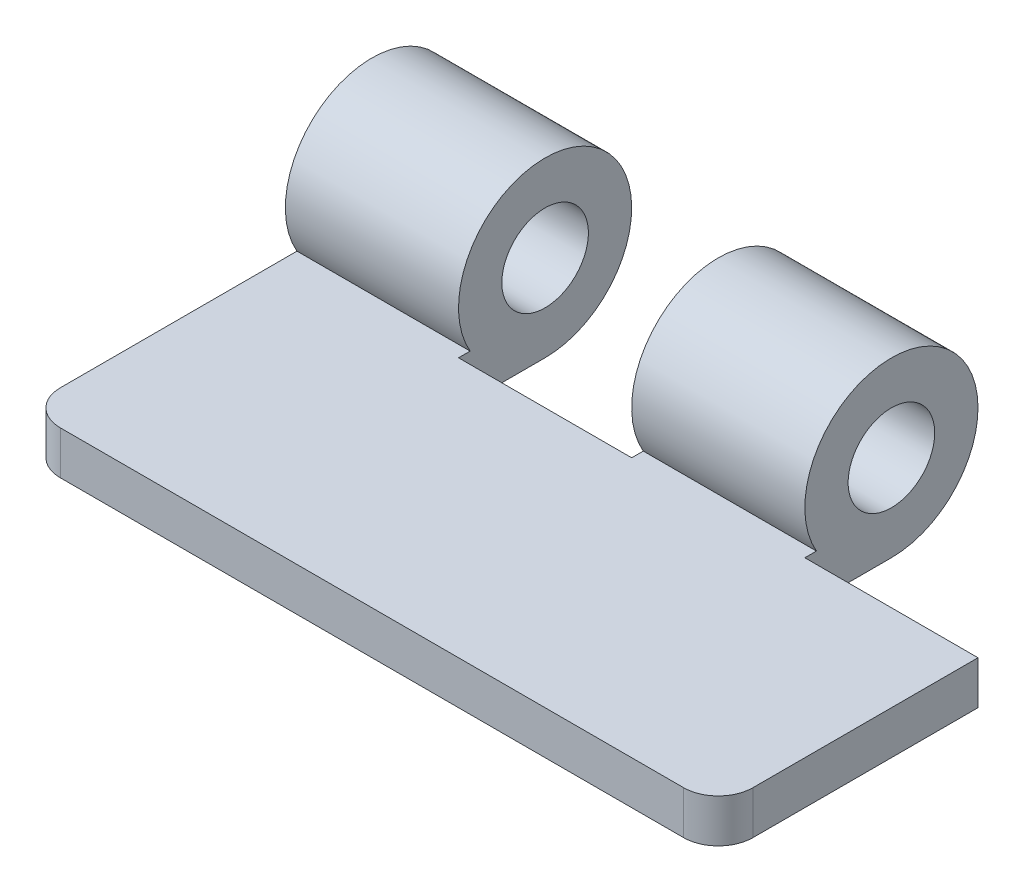
SolidWorks part; units mm, degrees
ref_plane "Front Plane" through (0, 0, 0) normal (0, 0, 1) x (1, 0, 0)
ref_plane "Top Plane" through (0, 0, 0) normal (0, 1, 0) x (1, 0, 0)
ref_plane "Right Plane" through (0, 0, 0) normal (1, 0, 0) x (0, 0, -1)
sketch "Sketch1" plane through (0, 0, 0) normal (0, 1, 0) x (1, 0, 0)
  line L0 (0, 9.9532) -> (-12.7, 9.9532)
  line L1 (25.4, -9.0968) -> (-25.4, -9.0968)
  line L2 (25.4, -9.0968) -> (25.4, 9.9532)
  line L3 (25.4, 9.9532) -> (12.7, 9.9532)
  line L4 (-25.4, -9.0968) -> (-25.4, 9.0968)
  line L7 (-12.7, 9.9532) -> (0, 9.9532) construction
  line L8 (12.7, 9.9532) -> (25.4, 9.9532) construction
  line L9 (-25.4, 9.0968) -> (-25.4, 16.3032)
  line L10 (-12.7, 4.7212) -> (-13.1825, 4.7212) construction
  line L14 (-25.4, 16.3032) -> (-12.7, 16.3032)
  line L15 (-12.7, 16.3032) -> (-12.7, 9.9532)
  line L16 (0, 9.9532) -> (0, 16.3032)
  line L17 (0, 16.3032) -> (12.7, 16.3032)
  line L18 (12.7, 16.3032) -> (12.7, 9.9532)
  point P0 (0, 0)
  dimension "D1" = 50.8
  dimension "D2" = 19.05
  dimension "D3" = 6.35
  dimension "D4" = 0
  dimension "D5" = 12.7
  dimension "D6" = 12.7
  dimension "D7" = 12.7
extrude "Boss-Extrude1" add sketch "Sketch1" along normal blind 3.175
sketch "Sketch2" plane through (0, 0, 0) normal (1, 0, 0) x (0, 0, -1)
  line L0 (16.3032, 0) -> (16.3032, 6.35) construction
  circle A0 centre (16.3032, 6.35) radius 6.35
  circle A1 centre (16.3032, 6.35) radius 3.175
  dimension "D1" = 12.7
  dimension "D2" = 6.35
extrude "Boss-Extrude2" add sketch "Sketch2" along normal blind 12.7
fillet "Fillet1" radius 2.54 2 edges at (25.4, 1.5875, 9.0968) (-25.4, 1.5875, 9.0968)
sketch "Sketch3" plane through (-25.4, 0, 0) normal (-1, 0, 0) x (0, 0, 1)
  line L3 (-16.3032, 0) -> (-9.9532, 0)
  line L4 (-9.9532, 0) -> (-9.9532, 3.175)
  line L5 (-9.9532, 3.175) -> (-10.804, 3.175)
  line L6 (-16.3032, 0) -> (-9.9532, 0)
  line L7 (-9.9532, 0) -> (-9.9532, 3.175)
  line L8 (-9.9532, 3.175) -> (-10.804, 3.175)
  circle A0 centre (-16.3032, 6.35) radius 3.175 construction
  arc A1 (-10.804, 3.175) -> (-16.3032, 0) centre (-16.3032, 6.35) ccw
  arc A2 (-10.804, 3.175) -> (-16.3032, 0) centre (-16.3032, 6.35) ccw
  circle A3 centre (-16.3032, 6.35) radius 3.175
  dimension "D1" = 0
extrude "Boss-Extrude3" add sketch "Sketch3" against normal blind 12.7
